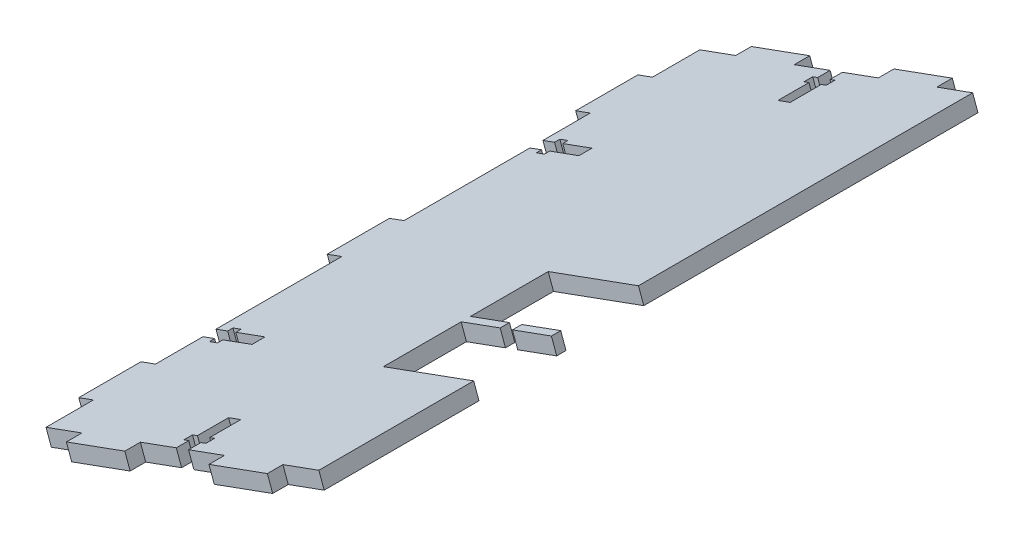
SolidWorks part; units mm, degrees
ref_plane "Front Plane" through (0, 0, 0) normal (0, 0, 1) x (1, 0, 0)
ref_plane "Top Plane" through (0, 0, 0) normal (0, 1, 0) x (1, 0, 0)
ref_plane "Right Plane" through (0, 0, 0) normal (1, 0, 0) x (0, 0, -1)
sketch "Sketch2" plane through (0, 0, 2) normal (0, 0, 1) x (1, 0, 0)
  line L17 (-920.8025, -330.7655) -> (-919.0937, -335.4644)
  line L18 (-920.8025, -330.7655) -> (-833.0379, -298.8492)
  line L19 (-919.0937, -335.4644) -> (-831.3291, -303.5481)
  line L20 (-833.0379, -298.8492) -> (-831.3291, -303.5481)
  line L21 (-919.0937, -335.4644) -> (-933.8149, -294.9835) construction
  line L22 (-605.128, -215.9681) -> (-925.5014, -332.4743) construction
  line L23 (-843.9975, -333.7826) -> (-729.3485, 31.655) construction
  point P8 (0, 0)
extrude "Boss-Extrude1" add sketch "Sketch2" along normal up to surface (210.2958 mm away)
sketch "Sketch4" plane through (0.3948, -1.0857, 0) normal (0.3418, -0.9398, 0) x (-0.9398, -0.3418, 0)
  line L0 (929.607, -2) -> (933.807, -2)
  line L1 (929.607, -2) -> (929.607, -6)
  line L2 (933.807, -2) -> (933.807, -6)
  line L3 (927.907, -6) -> (929.607, -6)
  line L4 (927.907, -6) -> (927.907, -8.8)
  line L5 (935.507, -6) -> (935.507, -8.8)
  line L6 (927.907, -8.8) -> (929.607, -8.8)
  line L7 (929.607, -8.8) -> (929.607, -18.8)
  line L8 (933.807, -8.8) -> (933.807, -18.8)
  line L9 (929.607, -18.8) -> (933.807, -18.8)
  line L10 (933.807, -8.8) -> (935.507, -8.8)
  line L11 (933.807, -6) -> (935.507, -6)
  line L14 (978.4009, -52.474) -> (978.4009, -56.674)
  line L25 (978.4009, -2) -> (885.0131, -2) construction
  line L26 (933.807, -212.2958) -> (929.607, -212.2958)
  line L27 (933.807, -212.2958) -> (933.807, -208.2958)
  line L28 (931.707, -18.8) -> (931.707, -2) construction
  line L29 (929.607, -212.2958) -> (929.607, -208.2958)
  line L30 (935.507, -208.2958) -> (933.807, -208.2958)
  line L31 (935.507, -208.2958) -> (935.507, -205.4958)
  line L32 (927.907, -208.2958) -> (927.907, -205.4958)
  line L33 (935.507, -205.4958) -> (933.807, -205.4958)
  line L34 (933.807, -205.4958) -> (933.807, -195.4958)
  line L35 (929.607, -205.4958) -> (929.607, -195.4958)
  line L36 (933.807, -195.4958) -> (929.607, -195.4958)
  line L37 (929.607, -205.4958) -> (927.907, -205.4958)
  line L38 (929.607, -208.2958) -> (927.907, -208.2958)
  line L39 (931.707, -195.4958) -> (931.707, -212.2958) construction
  line L40 (978.4009, -212.2958) -> (885.0131, -212.2958) construction
  line L41 (978.4009, -52.474) -> (974.4009, -52.474)
  line L42 (978.4009, -56.674) -> (974.4009, -56.674)
  line L43 (974.4009, -50.774) -> (974.4009, -52.474)
  line L44 (974.4009, -50.774) -> (971.6009, -50.774)
  line L45 (974.4009, -58.374) -> (971.6009, -58.374)
  line L46 (971.6009, -50.774) -> (971.6009, -52.474)
  line L47 (971.6009, -52.474) -> (961.6009, -52.474)
  line L48 (971.6009, -56.674) -> (961.6009, -56.674)
  line L49 (961.6009, -52.474) -> (961.6009, -56.674)
  line L50 (971.6009, -56.674) -> (971.6009, -58.374)
  line L51 (974.4009, -56.674) -> (974.4009, -58.374)
  line L52 (961.6009, -54.574) -> (978.4009, -54.574) construction
  line L55 (978.4009, -212.2958) -> (978.4009, -2) construction
  line L56 (978.4009, -2) -> (978.4009, -107.1479) construction
  line L57 (978.4009, -107.1479) -> (933.1322, -107.1479) construction
  line L58 (961.6009, -159.7219) -> (978.4009, -159.7219) construction
  line L59 (974.4009, -157.6219) -> (974.4009, -155.9219)
  line L60 (971.6009, -157.6219) -> (971.6009, -155.9219)
  line L61 (961.6009, -161.8219) -> (961.6009, -157.6219)
  line L62 (971.6009, -157.6219) -> (961.6009, -157.6219)
  line L63 (971.6009, -161.8219) -> (961.6009, -161.8219)
  line L64 (971.6009, -163.5219) -> (971.6009, -161.8219)
  line L65 (974.4009, -155.9219) -> (971.6009, -155.9219)
  line L66 (974.4009, -163.5219) -> (971.6009, -163.5219)
  line L67 (974.4009, -163.5219) -> (974.4009, -161.8219)
  line L68 (978.4009, -157.6219) -> (974.4009, -157.6219)
  line L69 (978.4009, -161.8219) -> (974.4009, -161.8219)
  line L70 (978.4009, -161.8219) -> (978.4009, -157.6219)
  line L71 (885.0131, -134.5) -> (898.357, -134.5)
  line L72 (885.0131, -134.5) -> (885.0131, -109.5)
  line L73 (915.9009, -134.5) -> (915.9009, -109.5)
  line L74 (885.0131, -109.5) -> (915.9009, -109.5)
  line L75 (885.0131, -212.2958) -> (885.0131, -2) construction
  line L76 (898.357, -134.5) -> (822.1723, -134.5) construction
  line L77 (853.4009, -109.5) -> (915.9009, -109.5) construction
  line L78 (915.9009, -109.5) -> (915.9009, -134.5) construction
  line L79 (885.0131, -137.5) -> (898.357, -137.5)
  line L80 (885.0131, -137.5) -> (885.0131, -162.5)
  line L81 (915.9009, -137.5) -> (915.9009, -162.5)
  line L82 (885.0131, -162.5) -> (915.9009, -162.5)
  line L83 (898.357, -134.5) -> (898.357, -137.5)
  line L84 (902.557, -134.5) -> (902.557, -137.5)
  line L85 (902.557, -134.5) -> (915.9009, -134.5)
  line L86 (902.557, -137.5) -> (915.9009, -137.5)
  dimension "D1" = 4.2
  dimension "D2" = 1.7
  dimension "D3" = 1.7
  dimension "D4" = 2.8
  dimension "D5" = 10
  dimension "D6" = 4
  dimension "D7" = 4.2
  dimension "D8" = 1.7
  dimension "D9" = 1.7
  dimension "D10" = 2.8
  dimension "D11" = 10
  dimension "D12" = 4
  dimension "D13" = 4.2
  dimension "D14" = 1.7
  dimension "D15" = 1.7
  dimension "D16" = 2.8
  dimension "D17" = 10
  dimension "D18" = 4
  dimension "D19" = 3
  dimension "D20" = 25
extrude "Cut-Extrude3" cut sketch "Sketch4" against normal through all
sketch "Sketch5" plane through (0.3948, -1.0857, 0) normal (0.3418, -0.9398, 0) x (0.9398, 0.3418, 0)
  line L0 (-966.1039, 212.2958) -> (-946.1039, 212.2958)
  line L1 (-966.1039, 212.2958) -> (-966.1039, 217.2958)
  line L2 (-946.1039, 212.2958) -> (-946.1039, 217.2958)
  line L3 (-966.1039, 217.2958) -> (-946.1039, 217.2958)
  line L4 (-978.4009, 212.2958) -> (-933.807, 212.2958) construction
  line L5 (-917.31, 212.2958) -> (-897.31, 212.2958)
  line L6 (-917.31, 212.2958) -> (-917.31, 217.2958)
  line L7 (-897.31, 212.2958) -> (-897.31, 217.2958)
  line L8 (-917.31, 217.2958) -> (-897.31, 217.2958)
  line L9 (-929.607, 212.2958) -> (-885.0131, 212.2958) construction
  line L10 (-978.4009, 177.0589) -> (-978.4009, 197.0589)
  line L11 (-978.4009, 177.0589) -> (-983.4009, 177.0589)
  line L12 (-978.4009, 197.0589) -> (-983.4009, 197.0589)
  line L13 (-983.4009, 177.0589) -> (-983.4009, 197.0589)
  line L14 (-978.4009, 212.2958) -> (-978.4009, 161.8219) construction
  line L15 (-978.4009, 97.1479) -> (-978.4009, 117.1479)
  line L16 (-978.4009, 97.1479) -> (-983.4009, 97.1479)
  line L17 (-978.4009, 117.1479) -> (-983.4009, 117.1479)
  line L18 (-983.4009, 97.1479) -> (-983.4009, 117.1479)
  line L19 (-978.4009, 157.6219) -> (-978.4009, 56.674) construction
  line L20 (-978.4009, 17.237) -> (-978.4009, 37.237)
  line L21 (-978.4009, 17.237) -> (-983.4009, 17.237)
  line L22 (-978.4009, 37.237) -> (-983.4009, 37.237)
  line L23 (-983.4009, 17.237) -> (-983.4009, 37.237)
  line L24 (-978.4009, 52.474) -> (-978.4009, 2) construction
  line L25 (-946.1039, 2) -> (-966.1039, 2)
  line L26 (-946.1039, 2) -> (-946.1039, -3)
  line L27 (-966.1039, 2) -> (-966.1039, -3)
  line L28 (-946.1039, -3) -> (-966.1039, -3)
  line L29 (-978.4009, 2) -> (-933.807, 2) construction
  line L30 (-897.31, 2) -> (-917.31, 2)
  line L31 (-897.31, 2) -> (-897.31, -3)
  line L32 (-917.31, 2) -> (-917.31, -3)
  line L33 (-897.31, -3) -> (-917.31, -3)
  line L34 (-929.607, 2) -> (-885.0131, 2) construction
  point P10 (-956.1039, 212.2958)
  point P11 (-907.31, 212.2958)
  point P16 (-978.4009, 187.0589)
  point P17 (0, 0)
  point P20 (-978.4009, 187.2823)
  point P23 (-978.4009, 107.1479)
  point P28 (0, 0)
  point P31 (-978.4009, 27.237)
  point P36 (0, 0)
  point P39 (-956.1039, 2)
  point P44 (0, 0)
  point P47 (0, 0)
  point P48 (-946.1039, 0.9605)
  point P49 (-907.31, 2)
  point P54 (0, 0)
  dimension "D1" = 5
  dimension "D2" = 20
  dimension "D3" = 5
  dimension "D4" = 20
  dimension "D5" = 5
  dimension "D6" = 20
  dimension "D7" = 5
  dimension "D8" = 20
  dimension "D9" = 5
  dimension "D10" = 20
  dimension "D11" = 5
  dimension "D12" = 20
  dimension "D13" = 5
  dimension "D14" = 20
extrude "Boss-Extrude2" add sketch "Sketch5" against normal blind 5
